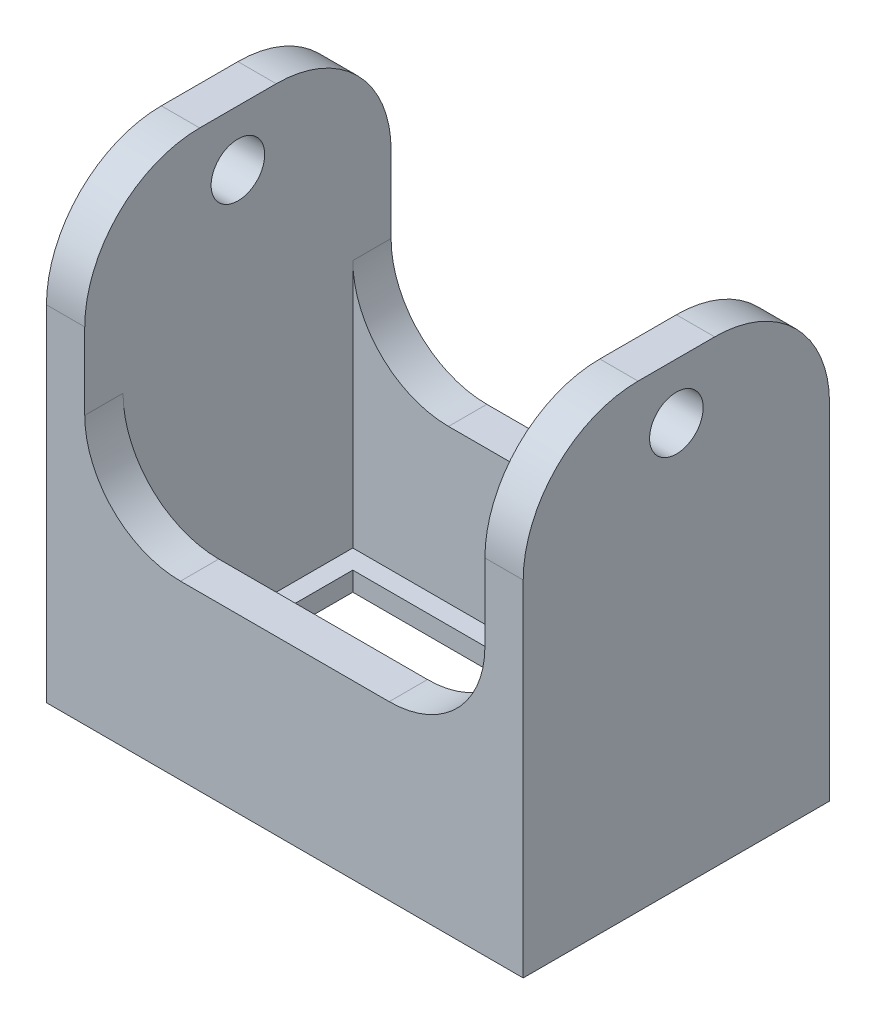
SolidWorks part; units mm, degrees
ref_plane "Front Plane" through (0, 0, 0) normal (0, 0, 1) x (1, 0, 0)
ref_plane "Top Plane" through (0, 0, 0) normal (0, 1, 0) x (1, 0, 0)
ref_plane "Right Plane" through (0, 0, 0) normal (1, 0, 0) x (0, 0, -1)
sketch "Sketch1" plane through (0, 0, 0) normal (0, 1, 0) x (1, 0, 0)
  line L0 (9.45, -5) -> (9.45, 5)
  line L1 (-12.45, -8) -> (12.45, -8)
  line L2 (-12.45, -8) -> (-12.45, 8)
  line L3 (-12.45, 8) -> (12.45, 8)
  line L4 (12.45, -8) -> (12.45, 8)
  line L5 (-12.45, -8) -> (12.45, 8) construction
  line L6 (-12.45, 8) -> (12.45, -8) construction
  line L7 (-9.45, 5) -> (9.45, 5)
  line L8 (-9.45, -5) -> (-9.45, 5)
  line L9 (-9.45, -5) -> (9.45, -5)
  point P0 (0, 0)
  dimension "D1" = 24.9
  dimension "D2" = 16
  dimension "D3" = 3
extrude "Boss-Extrude1" add sketch "Sketch1" along normal blind 1
sketch "Sketch2" plane through (0, 1, 0) normal (0, 1, 0) x (1, 0, 0)
  line L11 (-12.45, -8) -> (12.45, -8)
  line L12 (-12.45, -8) -> (-12.45, 8)
  line L13 (-12.45, 8) -> (12.45, 8)
  line L14 (-10.45, -6) -> (10.45, -6)
  line L15 (-10.45, 6) -> (-10.45, -6)
  line L16 (10.45, -6) -> (10.45, 6)
  line L17 (10.45, 6) -> (-10.45, 6)
  line L18 (-10.45, -6) -> (10.45, -6)
  line L19 (-10.45, 6) -> (-10.45, -6)
  line L20 (10.45, -6) -> (10.45, 6)
  line L21 (10.45, 6) -> (-10.45, 6)
  line L22 (12.45, -8) -> (12.45, 8)
  line L23 (-12.45, -8) -> (12.45, 8) construction
  line L24 (-12.45, 8) -> (12.45, -8) construction
  point P0 (0, 0)
  dimension "D1" = 2
extrude "Boss-Extrude2" add sketch "Sketch2" along normal blind 8
sketch "Sketch3" plane through (0, 9, 0) normal (0, 1, 0) x (1, 0, 0)
  line L0 (-12.45, -8) -> (12.45, -8) construction
  line L1 (-12.45, 8) -> (-10.45, 8)
  line L2 (-12.45, 8) -> (-12.45, -8)
  line L3 (-12.45, -8) -> (-10.45, -8)
  line L4 (-10.45, 8) -> (-10.45, -8)
  line L6 (12.45, 8) -> (10.45, 8)
  line L7 (12.45, 8) -> (12.45, -8)
  line L8 (12.45, -8) -> (10.45, -8)
  line L9 (10.45, 8) -> (10.45, -8)
  dimension "D1" = 2
  dimension "D2" = 2
extrude "Boss-Extrude3" add sketch "Sketch3" along normal blind 15
fillet "Fillet1" radius 5 4 edges at (10.45, 9, 7) (10.45, 9, -7)
sketch "Sketch4" plane through (12.45, 0, 0) normal (1, 0, 0) x (0, 0, -1)
  line L0 (0, 24) -> (0, 0) construction
  line L1 (-8, 24) -> (8, 24) construction
  line L2 (-8, 0) -> (8, 0) construction
  circle A0 centre (0, 21.1) radius 1.4
  dimension "D1" = 2.8
  dimension "D2" = 2.9
extrude "Cut-Extrude1" cut sketch "Sketch4" against normal up to surface (24.9 mm away) up to face at (-12.45, 12, 0)
fillet "Fillet2" radius 6 4 edges at (11.45, 24, -8) (11.45, 24, 8) (-11.45, 24, 8) (-11.45, 24, -8)
